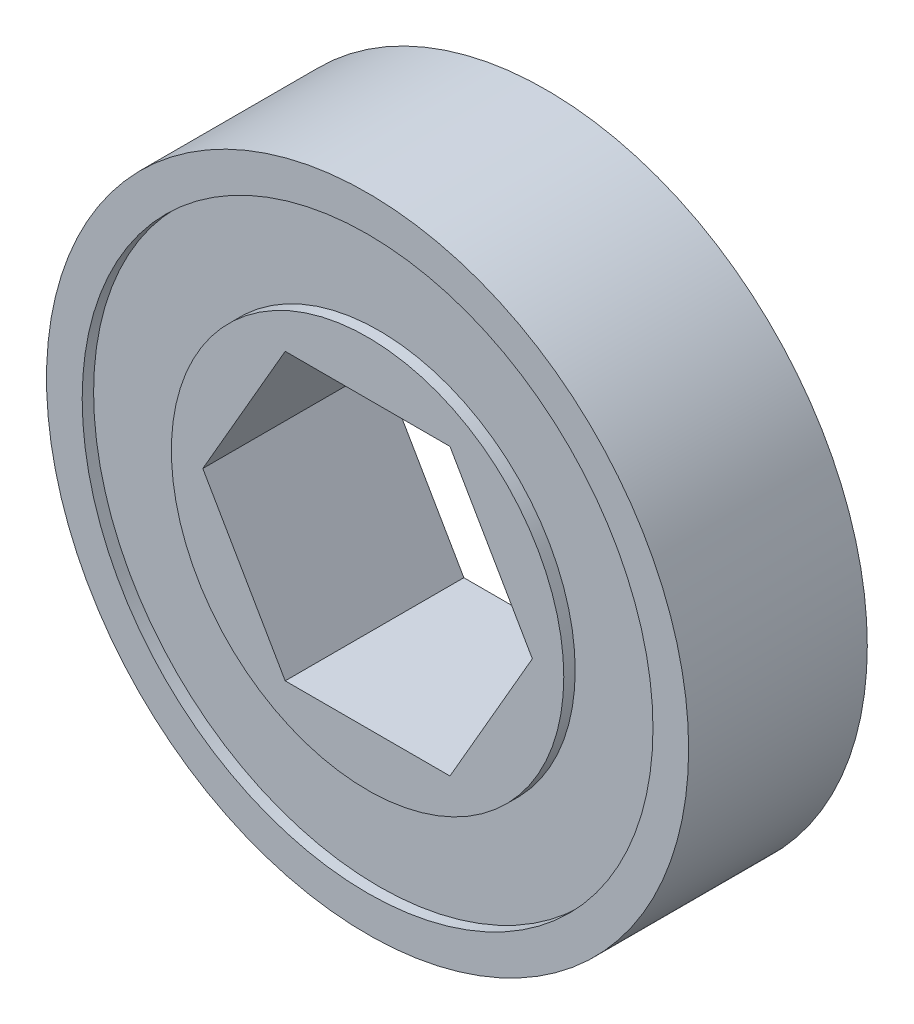
SolidWorks part; units mm, degrees
ref_plane "Front Plane" through (0, 0, 0) normal (0, 0, 1) x (1, 0, 0)
ref_plane "Top Plane" through (0, 0, 0) normal (0, 1, 0) x (1, 0, 0)
ref_plane "Right Plane" through (0, 0, 0) normal (1, 0, 0) x (0, 0, -1)
sketch "Sketch1" plane through (0, 0, 0) normal (0, 0, 1) x (1, 0, 0)
  line L1 (7.3323, 0) -> (3.6662, 6.35)
  line L2 (3.6662, 6.35) -> (-3.6662, 6.35)
  line L3 (-3.6662, 6.35) -> (-7.3323, 0)
  line L4 (-7.3323, 0) -> (-3.6662, -6.35)
  line L5 (-3.6662, -6.35) -> (3.6662, -6.35)
  line L6 (3.6662, -6.35) -> (7.3323, 0)
  circle A0 centre (0, 0) radius 14.2875
  circle A1 centre (0, 0) radius 6.35 construction
  dimension "D1" = 28.575
  dimension "D2" = 12.7
extrude "Boss-Extrude1" add sketch "Sketch1" along normal mid plane 7.9502
sketch "Sketch2" plane through (0, 0, 3.9751) normal (0, 0, 1) x (1, 0, 0)
  circle A0 centre (0, 0) radius 8.7312
  circle A1 centre (0, 0) radius 12.7
  dimension "D1" = 25.4
  dimension "D2" = 17.4625
extrude "Cut-Extrude1" cut sketch "Sketch2" against normal blind 0.508
mirror "Mirror1" about plane through (0, 0, 0) normal (0, 0, 1) of "Cut-Extrude1"
